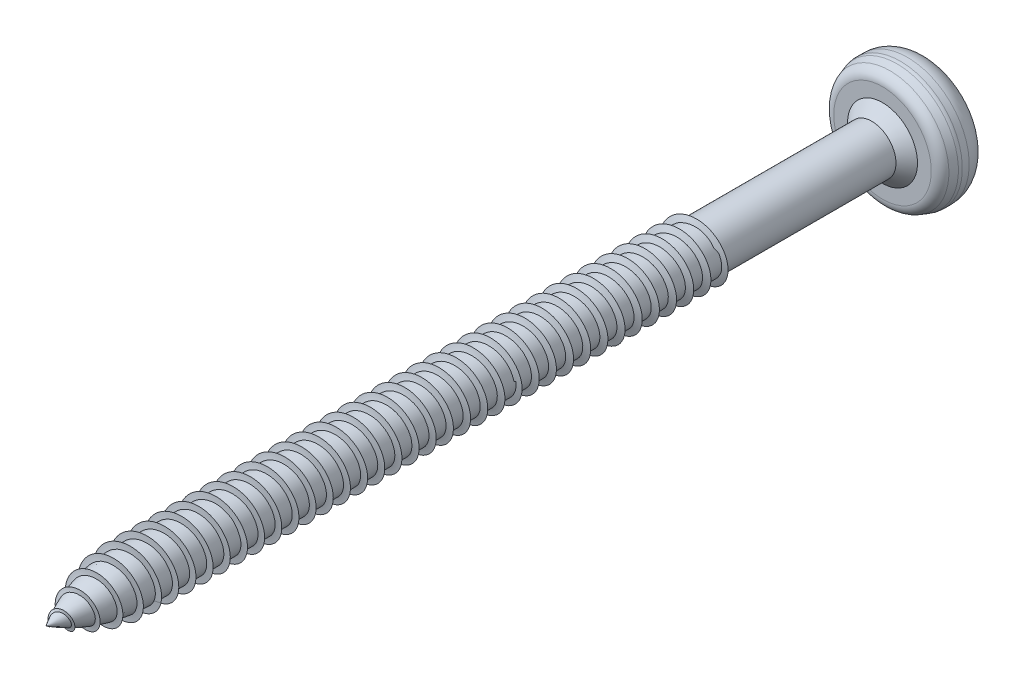
SolidWorks part; units mm, degrees
material "Rostfreier Stahl (ferritisch)"
ref_plane "Ebene vorne" through (0, 0, 0) normal (0, 0, 1) x (1, 0, 0)
ref_plane "Ebene oben" through (0, 0, 0) normal (0, 1, 0) x (1, 0, 0)
ref_plane "Ebene rechts" through (0, 0, 0) normal (1, 0, 0) x (0, 0, -1)
sketch "Skizze1" plane through (0, 0, 0) normal (1, 0, 0) x (0, 0, -1)
  line L0 (0, 0) -> (-87.1393, 0) construction
  line L1 (-0.0068, 3.4746) -> (-0.9378, 0)
  line L2 (-74, 2.25) -> (-5.3, 2.25)
  line L3 (-5.3, 2.25) -> (-4.3, 3.25)
  line L4 (-4.3, 3.25) -> (-4.3, 4.5292)
  line L5 (0, 3.75) -> (0, 3.5263)
  line L6 (-0.9378, 0) -> (-82, 0)
  line L7 (-3.6162, 5.4779) -> (-2.954, 5.6987)
  line L8 (-2.6377, 5.75) -> (-2, 5.75)
  arc A0 (-74, 2.25) -> (-82, 0) centre (-74, -13.0972) ccw
  arc A1 (-2.6377, 5.75) -> (-2.954, 5.6987) centre (-2.6377, 4.75) ccw
  arc A2 (-2, 5.75) -> (0, 3.75) centre (-2, 3.75) cw
  arc A3 (-4.3, 4.5292) -> (-3.6162, 5.4779) centre (-3.3, 4.5292) cw
  arc A5 (-0.0068, 3.4746) -> (0, 3.5263) centre (-0.2, 3.5263) ccw
  point P14 (0, 5.75)
  point P15 (-2.8, 5.75)
  point P19 (-4.3, 5.25)
  point P25 (0, 3.5)
  dimension "D8" = 0.5
  dimension "D9" = 2
  dimension "D12" = 0.2
  dimension "D14" = 1
  dimension "D1" = 45
  dimension "D2" = 1
  dimension "D3" = 11.5
  dimension "D4" = 4.3
  dimension "D5" = 4.5
  dimension "D6" = 8
  dimension "D7" = 82
  dimension "D10" = 15
  dimension "D11" = 7
  dimension "D13" = 1.5
revolve "Rotation1" add sketch "Skizze1" angle 360 about L0
ref_plane "Ebene5" through (0, 0, 82) normal (0, 0, 1) x (1, 0, 0)
sketch "Skizze15" plane through (0, 0, 0) normal (1, 0, 0) x (0, 0, -1)
  line L0 (-82, 0) -> (-20, 0)
  line L1 (-82, 6.325) -> (-82, -6.325) construction
  point P6 (-82, 0)
  dimension "D1" = 62
sketch "Skizze29" plane through (0, 0, 0) normal (1, 0, 0) x (0, 0, -1)
  line L1 (-74, 1.75) -> (-5.3, 1.75)
  line L2 (-5.3, 2.25) -> (-74, 2.25) construction
  line L3 (-74, 2.25) -> (-74, -2.25) construction
  line L4 (-5.3, 2.25) -> (-5.3, -2.25) construction
  arc A1 (-74, 1.75) -> (-82, 0) centre (-74, -17.4107) ccw
  dimension "D1" = 0.5
surface "Oberfläche-Rotation3" sketch "Skizze29" parameters "D1"=360
sketch "Skizze18" plane through (0, 0, 0) normal (1, 0, 0) x (0, 0, -1)
  line L1 (0, 0) -> (-82, 0) construction
  line L2 (-5.3, 2.8) -> (-74, 2.8)
  line L3 (-5.3, 2.8) -> (-74, 2.8)
  line L4 (-82, 6.325) -> (-82, -6.325) construction
  arc A0 (-74, 2.8) -> (-82, 0) centre (-74, -10.0286) ccw
  dimension "D2" = 5.6
  dimension "D1" = 0.55
surface "Oberfläche-Rotation2" sketch "Skizze18" parameters "D1"=360
sketch "Skizze27" plane through (0, 0, 82) normal (0, 0, 1) x (1, 0, 0)
  line L0 (0, 0) -> (0, 4)
  line L1 (0, 0) -> (3.9392, -0.6946)
  line L2 (0, 0) -> (-1.3681, -3.7588)
  circle A0 centre (0, 0) radius 4
  dimension "D1" = 8
  dimension "D2" = 100
  dimension "D3" = 100
surface "Oberfläche-Austragung13" parameters "D0"=14000
surface "Oberfläche-Trimmen6"
surface "Oberfläche-Trimmen7"
sketch "Skizze34" plane through (0, 0, 0) normal (1, 0, 0) x (0, 0, -1)
  line L0 (-82, 0) -> (-21.0647, 0)
  line L1 (-21.0647, 0) -> (-21.0647, -2.8)
  line L2 (-21.5039, -2.8) -> (-20.62, -2.8)
  spline S0 degree 2 poles (-20.0018, 1.3999) (-20.048, 1.8275) (-20.0886, 2.1449) (-20.2214, 3.184) (-20.3543, 2.6311) (-20.4871, 2.0782) (-20.62, 0.4862) (-20.7529, -1.1058) (-20.8857, -2.1449) (-21.0186, -3.184) (-21.1514, -2.6311) (-21.2843, -2.0782) (-21.4171, -0.4862) (-21.55, 1.1058) (-21.6829, 2.1449) (-21.8157, 3.184) (-21.9486, 2.6311) (-22.0814, 2.0782) (-22.2143, 0.4862) (-22.3471, -1.1058) (-22.48, -2.1449) (-22.6129, -3.184) (-22.7457, -2.6311) (-22.8786, -2.0782) (-23.0114, -0.4862) (-23.1443, 1.1058) (-23.2771, 2.1449) (-23.41, 3.184) (-23.5429, 2.6311) (-23.6757, 2.0782) (-23.8086, 0.4862) (-23.9414, -1.1058) (-24.0743, -2.1449) (-24.2071, -3.184) (-24.34, -2.6311) (-24.4729, -2.0782) (-24.6057, -0.4862) (-24.7386, 1.1058) (-24.8714, 2.1449) (-25.0043, 3.184) (-25.1371, 2.6311) (-25.27, 2.0782) (-25.4029, 0.4862) (-25.5357, -1.1058) (-25.6686, -2.1449) (-25.8014, -3.184) (-25.9343, -2.6311) (-26.0671, -2.0782) (-26.2, -0.4862) (-26.3329, 1.1058) (-26.4657, 2.1449) (-26.5986, 3.184) (-26.7314, 2.6311) (-26.8643, 2.0782) (-26.9971, 0.4862) (-27.13, -1.1058) (-27.2629, -2.1449) (-27.3957, -3.184) (-27.5286, -2.6311) (-27.6614, -2.0782) (-27.7943, -0.4862) (-27.9271, 1.1058) (-28.06, 2.1449) (-28.1929, 3.184) (-28.3257, 2.6311) (-28.4586, 2.0782) (-28.5914, 0.4862) (-28.7243, -1.1058) (-28.8571, -2.1449) (-28.99, -3.184) (-29.1229, -2.6311) (-29.2557, -2.0782) (-29.3886, -0.4862) (-29.5214, 1.1058) (-29.6543, 2.1449) (-29.7871, 3.184) (-29.92, 2.6311) (-30.0529, 2.0782) (-30.1857, 0.4862) (-30.3186, -1.1058) (-30.4514, -2.1449) (-30.5843, -3.184) (-30.7171, -2.6311) (-30.85, -2.0782) (-30.9829, -0.4862) (-31.1157, 1.1058) (-31.2486, 2.1449) (-31.3814, 3.184) (-31.5143, 2.6311) (-31.6471, 2.0782) (-31.78, 0.4862) (-31.9129, -1.1058) (-32.0457, -2.1449) (-32.1786, -3.184) (-32.3114, -2.6311) (-32.4443, -2.0782) (-32.5771, -0.4862) (-32.71, 1.1058) (-32.8429, 2.1449) (-32.9757, 3.184) (-33.1086, 2.6311) (-33.2414, 2.0782) (-33.3743, 0.4862) (-33.5071, -1.1058) (-33.64, -2.1449) (-33.7729, -3.184) (-33.9057, -2.6311) (-34.0386, -2.0782) (-34.1714, -0.4862) (-34.3043, 1.1058) (-34.4371, 2.1449) (-34.57, 3.184) (-34.7029, 2.6311) (-34.8357, 2.0782) (-34.9686, 0.4862) (-35.1014, -1.1058) (-35.2343, -2.1449) (-35.3671, -3.184) (-35.5, -2.6311) (-35.6329, -2.0782) (-35.7657, -0.4862) (-35.8986, 1.1058) (-36.0314, 2.1449) (-36.1643, 3.184) (-36.2971, 2.6311) (-36.43, 2.0782) (-36.5629, 0.4862) (-36.6957, -1.1058) (-36.8286, -2.1449) (-36.9614, -3.184) (-37.0943, -2.6311) (-37.2271, -2.0782) (-37.36, -0.4862) (-37.4929, 1.1058) (-37.6257, 2.1449) (-37.7586, 3.184) (-37.8914, 2.6311) (-38.0243, 2.0782) (-38.1571, 0.4862) (-38.29, -1.1058) (-38.4229, -2.1449) (-38.5557, -3.184) (-38.6886, -2.6311) (-38.8214, -2.0782) (-38.9543, -0.4862) (-39.0871, 1.1058) (-39.22, 2.1449) (-39.3529, 3.184) (-39.4857, 2.6311) (-39.6186, 2.0782) (-39.7514, 0.4862) (-39.8843, -1.1058) (-40.0171, -2.1449) (-40.15, -3.184) (-40.2829, -2.6311) (-40.4157, -2.0782) (-40.5486, -0.4862) (-40.6814, 1.1058) (-40.8143, 2.1449) (-40.9471, 3.184) (-41.08, 2.6311) (-41.2129, 2.0782) (-41.3457, 0.4862) (-41.4786, -1.1058) (-41.6114, -2.1449) (-41.7443, -3.184) (-41.8771, -2.6311) (-42.01, -2.0782) (-42.1429, -0.4862) (-42.2757, 1.1058) (-42.4086, 2.1449) (-42.5414, 3.184) (-42.6743, 2.6311) (-42.8071, 2.0782) (-42.94, 0.4862) (-43.0729, -1.1058) (-43.2057, -2.1449) (-43.3386, -3.184) (-43.4714, -2.6311) (-43.6043, -2.0782) (-43.7371, -0.4862) (-43.87, 1.1058) (-44.0029, 2.1449) (-44.1357, 3.184) (-44.2686, 2.6311) (-44.4014, 2.0782) (-44.5343, 0.4862) (-44.6671, -1.1058) (-44.8, -2.1449) (-44.9329, -3.184) (-45.0657, -2.6311) (-45.1986, -2.0782) (-45.3314, -0.4862) (-45.4643, 1.1058) (-45.5971, 2.1449) (-45.73, 3.184) (-45.8629, 2.6311) (-45.9957, 2.0782) (-46.1286, 0.4862) (-46.2614, -1.1058) (-46.3943, -2.1449) (-46.5271, -3.184) (-46.66, -2.6311) (-46.7929, -2.0782) (-46.9257, -0.4862) (-47.0586, 1.1058) (-47.1914, 2.1449) (-47.3243, 3.184) (-47.4571, 2.6311) (-47.59, 2.0782) (-47.7229, 0.4862) (-47.8557, -1.1058) (-47.9886, -2.1449) (-48.1214, -3.184) (-48.2543, -2.6311) (-48.3871, -2.0782) (-48.52, -0.4862) (-48.6529, 1.1058) (-48.7857, 2.1449) (-48.9186, 3.184) (-49.0514, 2.6311) (-49.1843, 2.0782) (-49.3171, 0.4862) (-49.45, -1.1058) (-49.5829, -2.1449) (-49.7157, -3.184) (-49.8486, -2.6311) (-49.9814, -2.0782) (-50.1143, -0.4862) (-50.2471, 1.1058) (-50.38, 2.1449) (-50.5129, 3.184) (-50.6457, 2.6311) (-50.7786, 2.0782) (-50.9114, 0.4862) (-51.0443, -1.1058) (-51.1771, -2.1449) (-51.31, -3.184) (-51.4429, -2.6311) (-51.5757, -2.0782) (-51.7086, -0.4862) (-51.8414, 1.1058) (-51.9743, 2.1449) (-52.1071, 3.184) (-52.24, 2.6311) (-52.3729, 2.0782) (-52.5057, 0.4862) (-52.6386, -1.1058) (-52.7714, -2.1449) (-52.9043, -3.184) (-53.0371, -2.6311) (-53.17, -2.0782) (-53.3029, -0.4862) (-53.4357, 1.1058) (-53.5686, 2.1449) (-53.7014, 3.184) (-53.8343, 2.6311) (-53.9671, 2.0782) (-54.1, 0.4862) (-54.2329, -1.1058) (-54.3657, -2.1449) (-54.4986, -3.184) (-54.6314, -2.6311) (-54.7643, -2.0782) (-54.8971, -0.4862) (-55.03, 1.1058) (-55.1629, 2.1449) (-55.2957, 3.184) (-55.4286, 2.6311) (-55.5614, 2.0782) (-55.6943, 0.4862) (-55.8271, -1.1058) (-55.96, -2.1449) (-56.0929, -3.184) (-56.2257, -2.6311) (-56.3586, -2.0782) (-56.4914, -0.4862) (-56.6243, 1.1058) (-56.7571, 2.1449) (-56.89, 3.184) (-57.0229, 2.6311) (-57.1557, 2.0782) (-57.2886, 0.4862) (-57.4214, -1.1058) (-57.5543, -2.1449) (-57.6871, -3.184) (-57.82, -2.6311) (-57.9529, -2.0782) (-58.0857, -0.4862) (-58.2186, 1.1058) (-58.3514, 2.1449) (-58.4843, 3.184) (-58.6171, 2.6311) (-58.75, 2.0782) (-58.8829, 0.4862) (-59.0157, -1.1058) (-59.1486, -2.1449) (-59.2814, -3.184) (-59.4143, -2.6311) (-59.5471, -2.0782) (-59.68, -0.4862) (-59.8129, 1.1058) (-59.9457, 2.1449) (-60.0786, 3.184) (-60.2114, 2.6311) (-60.3443, 2.0782) (-60.4771, 0.4862) (-60.61, -1.1058) (-60.7429, -2.1449) (-60.8757, -3.184) (-61.0086, -2.6311) (-61.1414, -2.0782) (-61.2743, -0.4862) (-61.4071, 1.1058) (-61.54, 2.1449) (-61.6729, 3.184) (-61.8057, 2.6311) (-61.9386, 2.0782) (-62.0714, 0.4862) (-62.2043, -1.1058) (-62.3371, -2.1449) (-62.47, -3.184) (-62.6029, -2.6311) (-62.7357, -2.0782) (-62.8686, -0.4862) (-63.0014, 1.1058) (-63.1343, 2.1449) (-63.2671, 3.184) (-63.4, 2.6311) (-63.5329, 2.0782) (-63.6657, 0.4862) (-63.7986, -1.1058) (-63.9314, -2.1449) (-64.0643, -3.184) (-64.1971, -2.6311) (-64.33, -2.0782) (-64.4629, -0.4862) (-64.5957, 1.1058) (-64.7286, 2.1449) (-64.8614, 3.184) (-64.9943, 2.6311) (-65.1271, 2.0782) (-65.26, 0.4862) (-65.3929, -1.1058) (-65.5257, -2.1449) (-65.6586, -3.184) (-65.7914, -2.6311) (-65.9243, -2.0782) (-66.0571, -0.4862) (-66.19, 1.1058) (-66.3229, 2.1449) (-66.4557, 3.184) (-66.5886, 2.6311) (-66.7214, 2.0782) (-66.8543, 0.4862) (-66.9871, -1.1058) (-67.12, -2.1449) (-67.2529, -3.184) (-67.3857, -2.6311) (-67.5186, -2.0782) (-67.6514, -0.4862) (-67.7843, 1.1058) (-67.9171, 2.1449) (-68.05, 3.184) (-68.1829, 2.6311) (-68.3157, 2.0782) (-68.4486, 0.4862) (-68.5814, -1.1058) (-68.7143, -2.1449) (-68.8471, -3.184) (-68.98, -2.6311) (-69.1129, -2.0782) (-69.2457, -0.4862) (-69.3786, 1.1058) (-69.5114, 2.1449) (-69.6443, 3.184) (-69.7771, 2.6311) (-69.91, 2.0782) (-70.0429, 0.4862) (-70.1757, -1.1058) (-70.3086, -2.1449) (-70.4414, -3.184) (-70.5743, -2.6311) (-70.7071, -2.0782) (-70.84, -0.4862) (-70.9729, 1.1058) (-71.1057, 2.1449) (-71.2386, 3.184) (-71.3714, 2.6311) (-71.5043, 2.0782) (-71.6371, 0.4862) (-71.77, -1.1058) (-71.9029, -2.1449) (-72.0357, -3.184) (-72.1686, -2.6311) (-72.3014, -2.0782) (-72.4343, -0.4862) (-72.5671, 1.1058) (-72.7, 2.1449) (-72.8329, 3.184) (-72.9657, 2.6311) (-73.0986, 2.0782) (-73.2314, 0.4862) (-73.3643, -1.1058) (-73.4971, -2.1449) (-73.63, -3.184) (-73.7629, -2.6311) (-73.8779, -2.1525) (-74, -0.8136) knots 0.128712 0.128712 0.128712 0.130151 0.130151 0.134424 0.134424 0.138698 0.138698 0.142971 0.142971 0.147245 0.147245 0.151518 0.151518 0.155792 0.155792 0.160065 0.160065 0.164339 0.164339 0.168612 0.168612 0.172886 0.172886 0.177159 0.177159 0.181433 0.181433 0.185706 0.185706 0.18998 0.18998 0.194253 0.194253 0.198527 0.198527 0.2028 0.2028 0.207074 0.207074 0.211347 0.211347 0.215621 0.215621 0.219894 0.219894 0.224168 0.224168 0.228441 0.228441 0.232715 0.232715 0.236988 0.236988 0.241262 0.241262 0.245535 0.245535 0.249809 0.249809 0.254082 0.254082 0.258356 0.258356 0.262629 0.262629 0.266903 0.266903 0.271176 0.271176 0.27545 0.27545 0.279723 0.279723 0.283997 0.283997 0.28827 0.28827 0.292544 0.292544 0.296817 0.296817 0.301091 0.301091 0.305364 0.305364 0.309638 0.309638 0.313911 0.313911 0.318185 0.318185 0.322458 0.322458 0.326732 0.326732 0.331005 0.331005 0.335279 0.335279 0.339553 0.339553 0.343826 0.343826 0.3481 0.3481 0.352373 0.352373 0.356647 0.356647 0.36092 0.36092 0.365194 0.365194 0.369467 0.369467 0.373741 0.373741 0.378014 0.378014 0.382288 0.382288 0.386561 0.386561 0.390835 0.390835 0.395108 0.395108 0.399382 0.399382 0.403655 0.403655 0.407929 0.407929 0.412202 0.412202 0.416476 0.416476 0.420749 0.420749 0.425023 0.425023 0.429296 0.429296 0.43357 0.43357 0.437843 0.437843 0.442117 0.442117 0.44639 0.44639 0.450664 0.450664 0.454937 0.454937 0.459211 0.459211 0.463484 0.463484 0.467758 0.467758 0.472031 0.472031 0.476305 0.476305 0.480578 0.480578 0.484852 0.484852 0.489125 0.489125 0.493399 0.493399 0.497672 0.497672 0.501946 0.501946 0.506219 0.506219 0.510493 0.510493 0.514766 0.514766 0.51904 0.51904 0.523313 0.523313 0.527587 0.527587 0.53186 0.53186 0.536134 0.536134 0.540407 0.540407 0.544681 0.544681 0.548954 0.548954 0.553228 0.553228 0.557501 0.557501 0.561775 0.561775 0.566048 0.566048 0.570322 0.570322 0.574595 0.574595 0.578869 0.578869 0.583142 0.583142 0.587416 0.587416 0.591689 0.591689 0.595963 0.595963 0.600236 0.600236 0.60451 0.60451 0.608783 0.608783 0.613057 0.613057 0.61733 0.61733 0.621604 0.621604 0.625877 0.625877 0.630151 0.630151 0.634424 0.634424 0.638698 0.638698 0.642971 0.642971 0.647245 0.647245 0.651518 0.651518 0.655792 0.655792 0.660065 0.660065 0.664339 0.664339 0.668612 0.668612 0.672886 0.672886 0.677159 0.677159 0.681433 0.681433 0.685706 0.685706 0.68998 0.68998 0.694253 0.694253 0.698527 0.698527 0.7028 0.7028 0.707074 0.707074 0.711347 0.711347 0.715621 0.715621 0.719894 0.719894 0.724168 0.724168 0.728441 0.728441 0.732715 0.732715 0.736988 0.736988 0.741262 0.741262 0.745535 0.745535 0.749809 0.749809 0.754082 0.754082 0.758356 0.758356 0.762629 0.762629 0.766903 0.766903 0.771176 0.771176 0.77545 0.77545 0.779723 0.779723 0.783997 0.783997 0.78827 0.78827 0.792544 0.792544 0.796817 0.796817 0.801091 0.801091 0.805364 0.805364 0.809638 0.809638 0.813911 0.813911 0.818185 0.818185 0.822458 0.822458 0.826732 0.826732 0.831005 0.831005 0.835279 0.835279 0.839553 0.839553 0.843826 0.843826 0.8481 0.8481 0.852373 0.852373 0.856647 0.856647 0.86092 0.86092 0.865194 0.865194 0.869467 0.869467 0.873741 0.873741 0.878014 0.878014 0.882288 0.882288 0.886561 0.886561 0.890835 0.890835 0.895108 0.895108 0.899382 0.899382 0.903655 0.903655 0.907929 0.907929 0.912202 0.912202 0.916476 0.916476 0.920749 0.920749 0.925023 0.925023 0.929296 0.929296 0.93357 0.93357 0.937843 0.937843 0.942117 0.942117 0.94639 0.94639 0.950664 0.950664 0.954937 0.954937 0.959211 0.959211 0.963484 0.963484 0.967758 0.967758 0.972031 0.972031 0.976305 0.976305 0.980578 0.980578 0.984852 0.984852 0.989125 0.989125 0.993399 0.993399 0.997166 0.997166 0.997166 weights 0.940152 0.954881 1 0.866025 1 0.866025 1 0.866025 1 0.866025 1 0.866025 1 0.866025 1 0.866025 1 0.866025 1 0.866025 1 0.866025 1 0.866025 1 0.866025 1 0.866025 1 0.866025 1 0.866025 1 0.866025 1 0.866025 1 0.866025 1 0.866025 1 0.866025 1 0.866025 1 0.866025 1 0.866025 1 0.866025 1 0.866025 1 0.866025 1 0.866025 1 0.866025 1 0.866025 1 0.866025 1 0.866025 1 0.866025 1 0.866025 1 0.866025 1 0.866025 1 0.866025 1 0.866025 1 0.866025 1 0.866025 1 0.866025 1 0.866025 1 0.866025 1 0.866025 1 0.866025 1 0.866025 1 0.866025 1 0.866025 1 0.866025 1 0.866025 1 0.866025 1 0.866025 1 0.866025 1 0.866025 1 0.866025 1 0.866025 1 0.866025 1 0.866025 1 0.866025 1 0.866025 1 0.866025 1 0.866025 1 0.866025 1 0.866025 1 0.866025 1 0.866025 1 0.866025 1 0.866025 1 0.866025 1 0.866025 1 0.866025 1 0.866025 1 0.866025 1 0.866025 1 0.866025 1 0.866025 1 0.866025 1 0.866025 1 0.866025 1 0.866025 1 0.866025 1 0.866025 1 0.866025 1 0.866025 1 0.866025 1 0.866025 1 0.866025 1 0.866025 1 0.866025 1 0.866025 1 0.866025 1 0.866025 1 0.866025 1 0.866025 1 0.866025 1 0.866025 1 0.866025 1 0.866025 1 0.866025 1 0.866025 1 0.866025 1 0.866025 1 0.866025 1 0.866025 1 0.866025 1 0.866025 1 0.866025 1 0.866025 1 0.866025 1 0.866025 1 0.866025 1 0.866025 1 0.866025 1 0.866025 1 0.866025 1 0.866025 1 0.866025 1 0.866025 1 0.866025 1 0.866025 1 0.866025 1 0.866025 1 0.866025 1 0.866025 1 0.866025 1 0.866025 1 0.866025 1 0.866025 1 0.866025 1 0.866025 1 0.866025 1 0.866025 1 0.866025 1 0.866025 1 0.866025 1 0.866025 1 0.866025 1 0.866025 1 0.866025 1 0.866025 1 0.866025 1 0.866025 1 0.866025 1 0.866025 1 0.866025 1 0.866025 1 0.866025 1 0.866025 1 0.866025 1 0.866025 1 0.866025 1 0.866025 1 0.866025 1 0.866025 1 0.866025 1 0.866025 1 0.866025 1 0.866025 1 0.866025 1 0.866025 1 0.866025 1 0.866025 1 0.866025 1 0.866025 1 0.866025 1 0.866025 1 0.866025 1 0.866025 1 0.866025 1 0.866025 1 0.866025 1 0.866025 1 0.866025 1 0.866025 1 0.866025 1 0.866025 1 0.866025 1 0.866025 1 0.866025 1 0.866025 1 0.866025 1 0.866025 1 0.866025 1 0.866025 1 0.866025 1 0.866025 1 0.866025 1 0.866025 1 0.866025 1 0.866025 1 0.866025 1 0.866025 1 0.866025 1 0.866025 1 0.866025 1 0.866025 1 0.866025 1 0.866025 1 0.866025 1 0.866025 1 0.866025 1 0.866025 1 0.866025 1 0.881903 0.972008 construction
  spline S1 degree 2 poles (-74, -2.4972) (-73.8779, -1.8643) (-73.7629, -0.4862) (-73.63, 1.1058) (-73.4971, 2.1449) (-73.3643, 3.184) (-73.2314, 2.6311) (-73.0986, 2.0782) (-72.9657, 0.4862) (-72.8329, -1.1058) (-72.7, -2.1449) (-72.5671, -3.184) (-72.4343, -2.6311) (-72.3014, -2.0782) (-72.1686, -0.4862) (-72.0357, 1.1058) (-71.9029, 2.1449) (-71.77, 3.184) (-71.6371, 2.6311) (-71.5043, 2.0782) (-71.3714, 0.4862) (-71.2386, -1.1058) (-71.1057, -2.1449) (-70.9729, -3.184) (-70.84, -2.6311) (-70.7071, -2.0782) (-70.5743, -0.4862) (-70.4414, 1.1058) (-70.3086, 2.1449) (-70.1757, 3.184) (-70.0429, 2.6311) (-69.91, 2.0782) (-69.7771, 0.4862) (-69.6443, -1.1058) (-69.5114, -2.1449) (-69.3786, -3.184) (-69.2457, -2.6311) (-69.1129, -2.0782) (-68.98, -0.4862) (-68.8471, 1.1058) (-68.7143, 2.1449) (-68.5814, 3.184) (-68.4486, 2.6311) (-68.3157, 2.0782) (-68.1829, 0.4862) (-68.05, -1.1058) (-67.9171, -2.1449) (-67.7843, -3.184) (-67.6514, -2.6311) (-67.5186, -2.0782) (-67.3857, -0.4862) (-67.2529, 1.1058) (-67.12, 2.1449) (-66.9871, 3.184) (-66.8543, 2.6311) (-66.7214, 2.0782) (-66.5886, 0.4862) (-66.4557, -1.1058) (-66.3229, -2.1449) (-66.19, -3.184) (-66.0571, -2.6311) (-65.9243, -2.0782) (-65.7914, -0.4862) (-65.6586, 1.1058) (-65.5257, 2.1449) (-65.3929, 3.184) (-65.26, 2.6311) (-65.1271, 2.0782) (-64.9943, 0.4862) (-64.8614, -1.1058) (-64.7286, -2.1449) (-64.5957, -3.184) (-64.4629, -2.6311) (-64.33, -2.0782) (-64.1971, -0.4862) (-64.0643, 1.1058) (-63.9314, 2.1449) (-63.7986, 3.184) (-63.6657, 2.6311) (-63.5329, 2.0782) (-63.4, 0.4862) (-63.2671, -1.1058) (-63.1343, -2.1449) (-63.0014, -3.184) (-62.8686, -2.6311) (-62.7357, -2.0782) (-62.6029, -0.4862) (-62.47, 1.1058) (-62.3371, 2.1449) (-62.2043, 3.184) (-62.0714, 2.6311) (-61.9386, 2.0782) (-61.8057, 0.4862) (-61.6729, -1.1058) (-61.54, -2.1449) (-61.4071, -3.184) (-61.2743, -2.6311) (-61.1414, -2.0782) (-61.0086, -0.4862) (-60.8757, 1.1058) (-60.7429, 2.1449) (-60.61, 3.184) (-60.4771, 2.6311) (-60.3443, 2.0782) (-60.2114, 0.4862) (-60.0786, -1.1058) (-59.9457, -2.1449) (-59.8129, -3.184) (-59.68, -2.6311) (-59.5471, -2.0782) (-59.4143, -0.4862) (-59.2814, 1.1058) (-59.1486, 2.1449) (-59.0157, 3.184) (-58.8829, 2.6311) (-58.75, 2.0782) (-58.6171, 0.4862) (-58.4843, -1.1058) (-58.3514, -2.1449) (-58.2186, -3.184) (-58.0857, -2.6311) (-57.9529, -2.0782) (-57.82, -0.4862) (-57.6871, 1.1058) (-57.5543, 2.1449) (-57.4214, 3.184) (-57.2886, 2.6311) (-57.1557, 2.0782) (-57.0229, 0.4862) (-56.89, -1.1058) (-56.7571, -2.1449) (-56.6243, -3.184) (-56.4914, -2.6311) (-56.3586, -2.0782) (-56.2257, -0.4862) (-56.0929, 1.1058) (-55.96, 2.1449) (-55.8271, 3.184) (-55.6943, 2.6311) (-55.5614, 2.0782) (-55.4286, 0.4862) (-55.2957, -1.1058) (-55.1629, -2.1449) (-55.03, -3.184) (-54.8971, -2.6311) (-54.7643, -2.0782) (-54.6314, -0.4862) (-54.4986, 1.1058) (-54.3657, 2.1449) (-54.2329, 3.184) (-54.1, 2.6311) (-53.9671, 2.0782) (-53.8343, 0.4862) (-53.7014, -1.1058) (-53.5686, -2.1449) (-53.4357, -3.184) (-53.3029, -2.6311) (-53.17, -2.0782) (-53.0371, -0.4862) (-52.9043, 1.1058) (-52.7714, 2.1449) (-52.6386, 3.184) (-52.5057, 2.6311) (-52.3729, 2.0782) (-52.24, 0.4862) (-52.1071, -1.1058) (-51.9743, -2.1449) (-51.8414, -3.184) (-51.7086, -2.6311) (-51.5757, -2.0782) (-51.4429, -0.4862) (-51.31, 1.1058) (-51.1771, 2.1449) (-51.0443, 3.184) (-50.9114, 2.6311) (-50.7786, 2.0782) (-50.6457, 0.4862) (-50.5129, -1.1058) (-50.38, -2.1449) (-50.2471, -3.184) (-50.1143, -2.6311) (-49.9814, -2.0782) (-49.8486, -0.4862) (-49.7157, 1.1058) (-49.5829, 2.1449) (-49.45, 3.184) (-49.3171, 2.6311) (-49.1843, 2.0782) (-49.0514, 0.4862) (-48.9186, -1.1058) (-48.7857, -2.1449) (-48.6529, -3.184) (-48.52, -2.6311) (-48.3871, -2.0782) (-48.2543, -0.4862) (-48.1214, 1.1058) (-47.9886, 2.1449) (-47.8557, 3.184) (-47.7229, 2.6311) (-47.59, 2.0782) (-47.4571, 0.4862) (-47.3243, -1.1058) (-47.1914, -2.1449) (-47.0586, -3.184) (-46.9257, -2.6311) (-46.7929, -2.0782) (-46.66, -0.4862) (-46.5271, 1.1058) (-46.3943, 2.1449) (-46.2614, 3.184) (-46.1286, 2.6311) (-45.9957, 2.0782) (-45.8629, 0.4862) (-45.73, -1.1058) (-45.5971, -2.1449) (-45.4643, -3.184) (-45.3314, -2.6311) (-45.1986, -2.0782) (-45.0657, -0.4862) (-44.9329, 1.1058) (-44.8, 2.1449) (-44.6671, 3.184) (-44.5343, 2.6311) (-44.4014, 2.0782) (-44.2686, 0.4862) (-44.1357, -1.1058) (-44.0029, -2.1449) (-43.87, -3.184) (-43.7371, -2.6311) (-43.6043, -2.0782) (-43.4714, -0.4862) (-43.3386, 1.1058) (-43.2057, 2.1449) (-43.0729, 3.184) (-42.94, 2.6311) (-42.8071, 2.0782) (-42.6743, 0.4862) (-42.5414, -1.1058) (-42.4086, -2.1449) (-42.2757, -3.184) (-42.1429, -2.6311) (-42.01, -2.0782) (-41.8771, -0.4862) (-41.7443, 1.1058) (-41.6114, 2.1449) (-41.4786, 3.184) (-41.3457, 2.6311) (-41.2129, 2.0782) (-41.08, 0.4862) (-40.9471, -1.1058) (-40.8143, -2.1449) (-40.6814, -3.184) (-40.5486, -2.6311) (-40.4157, -2.0782) (-40.2829, -0.4862) (-40.15, 1.1058) (-40.0171, 2.1449) (-39.8843, 3.184) (-39.7514, 2.6311) (-39.6186, 2.0782) (-39.4857, 0.4862) (-39.3529, -1.1058) (-39.22, -2.1449) (-39.0871, -3.184) (-38.9543, -2.6311) (-38.8214, -2.0782) (-38.6886, -0.4862) (-38.5557, 1.1058) (-38.4229, 2.1449) (-38.29, 3.184) (-38.1571, 2.6311) (-38.0243, 2.0782) (-37.8914, 0.4862) (-37.7586, -1.1058) (-37.6257, -2.1449) (-37.4929, -3.184) (-37.36, -2.6311) (-37.2271, -2.0782) (-37.0943, -0.4862) (-36.9614, 1.1058) (-36.8286, 2.1449) (-36.6957, 3.184) (-36.5629, 2.6311) (-36.43, 2.0782) (-36.2971, 0.4862) (-36.1643, -1.1058) (-36.0314, -2.1449) (-35.8986, -3.184) (-35.7657, -2.6311) (-35.6329, -2.0782) (-35.5, -0.4862) (-35.3671, 1.1058) (-35.2343, 2.1449) (-35.1014, 3.184) (-34.9686, 2.6311) (-34.8357, 2.0782) (-34.7029, 0.4862) (-34.57, -1.1058) (-34.4371, -2.1449) (-34.3043, -3.184) (-34.1714, -2.6311) (-34.0386, -2.0782) (-33.9057, -0.4862) (-33.7729, 1.1058) (-33.64, 2.1449) (-33.5071, 3.184) (-33.3743, 2.6311) (-33.2414, 2.0782) (-33.1086, 0.4862) (-32.9757, -1.1058) (-32.8429, -2.1449) (-32.71, -3.184) (-32.5771, -2.6311) (-32.4443, -2.0782) (-32.3114, -0.4862) (-32.1786, 1.1058) (-32.0457, 2.1449) (-31.9129, 3.184) (-31.78, 2.6311) (-31.6471, 2.0782) (-31.5143, 0.4862) (-31.3814, -1.1058) (-31.2486, -2.1449) (-31.1157, -3.184) (-30.9829, -2.6311) (-30.85, -2.0782) (-30.7171, -0.4862) (-30.5843, 1.1058) (-30.4514, 2.1449) (-30.3186, 3.184) (-30.1857, 2.6311) (-30.0529, 2.0782) (-29.92, 0.4862) (-29.7871, -1.1058) (-29.6543, -2.1449) (-29.5214, -3.184) (-29.3886, -2.6311) (-29.2557, -2.0782) (-29.1229, -0.4862) (-28.99, 1.1058) (-28.8571, 2.1449) (-28.7243, 3.184) (-28.5914, 2.6311) (-28.4586, 2.0782) (-28.3257, 0.4862) (-28.1929, -1.1058) (-28.06, -2.1449) (-27.9271, -3.184) (-27.7943, -2.6311) (-27.6614, -2.0782) (-27.5286, -0.4862) (-27.3957, 1.1058) (-27.2629, 2.1449) (-27.13, 3.184) (-26.9971, 2.6311) (-26.8643, 2.0782) (-26.7314, 0.4862) (-26.5986, -1.1058) (-26.4657, -2.1449) (-26.3329, -3.184) (-26.2, -2.6311) (-26.0671, -2.0782) (-25.9343, -0.4862) (-25.8014, 1.1058) (-25.6686, 2.1449) (-25.5357, 3.184) (-25.4029, 2.6311) (-25.27, 2.0782) (-25.1371, 0.4862) (-25.0043, -1.1058) (-24.8714, -2.1449) (-24.7386, -3.184) (-24.6057, -2.6311) (-24.4729, -2.0782) (-24.34, -0.4862) (-24.2071, 1.1058) (-24.0743, 2.1449) (-23.9414, 3.184) (-23.8086, 2.6311) (-23.6757, 2.0782) (-23.5429, 0.4862) (-23.41, -1.1058) (-23.2771, -2.1449) (-23.1443, -3.184) (-23.0114, -2.6311) (-22.8786, -2.0782) (-22.7457, -0.4862) (-22.6129, 1.1058) (-22.48, 2.1449) (-22.3471, 3.184) (-22.2143, 2.6311) (-22.0814, 2.0782) (-21.9486, 0.4862) (-21.8157, -1.1058) (-21.6829, -2.1449) (-21.55, -3.184) (-21.4171, -2.6311) (-21.2843, -2.0782) (-21.1514, -0.4862) (-21.0186, 1.1058) (-20.8857, 2.1449) (-20.7529, 3.184) (-20.62, 2.6311) (-20.4871, 2.0782) (-20.3543, 0.4862) (-20.2214, -1.1058) (-20.0886, -2.1449) (-20.048, -2.4623) (-20.0018, -2.6312) knots 0.128712 0.128712 0.128712 0.132479 0.132479 0.136752 0.136752 0.141026 0.141026 0.145299 0.145299 0.149573 0.149573 0.153846 0.153846 0.15812 0.15812 0.162393 0.162393 0.166667 0.166667 0.17094 0.17094 0.175214 0.175214 0.179487 0.179487 0.183761 0.183761 0.188034 0.188034 0.192308 0.192308 0.196581 0.196581 0.200855 0.200855 0.205128 0.205128 0.209402 0.209402 0.213675 0.213675 0.217949 0.217949 0.222222 0.222222 0.226496 0.226496 0.230769 0.230769 0.235043 0.235043 0.239316 0.239316 0.24359 0.24359 0.247863 0.247863 0.252137 0.252137 0.25641 0.25641 0.260684 0.260684 0.264957 0.264957 0.269231 0.269231 0.273504 0.273504 0.277778 0.277778 0.282051 0.282051 0.286325 0.286325 0.290598 0.290598 0.294872 0.294872 0.299145 0.299145 0.303419 0.303419 0.307692 0.307692 0.311966 0.311966 0.316239 0.316239 0.320513 0.320513 0.324786 0.324786 0.32906 0.32906 0.333333 0.333333 0.337607 0.337607 0.34188 0.34188 0.346154 0.346154 0.350427 0.350427 0.354701 0.354701 0.358974 0.358974 0.363248 0.363248 0.367521 0.367521 0.371795 0.371795 0.376068 0.376068 0.380342 0.380342 0.384615 0.384615 0.388889 0.388889 0.393162 0.393162 0.397436 0.397436 0.401709 0.401709 0.405983 0.405983 0.410256 0.410256 0.41453 0.41453 0.418803 0.418803 0.423077 0.423077 0.42735 0.42735 0.431624 0.431624 0.435897 0.435897 0.440171 0.440171 0.444444 0.444444 0.448718 0.448718 0.452991 0.452991 0.457265 0.457265 0.461538 0.461538 0.465812 0.465812 0.470085 0.470085 0.474359 0.474359 0.478632 0.478632 0.482906 0.482906 0.487179 0.487179 0.491453 0.491453 0.495726 0.495726 0.5 0.5 0.504274 0.504274 0.508547 0.508547 0.512821 0.512821 0.517094 0.517094 0.521368 0.521368 0.525641 0.525641 0.529915 0.529915 0.534188 0.534188 0.538462 0.538462 0.542735 0.542735 0.547009 0.547009 0.551282 0.551282 0.555556 0.555556 0.559829 0.559829 0.564103 0.564103 0.568376 0.568376 0.57265 0.57265 0.576923 0.576923 0.581197 0.581197 0.58547 0.58547 0.589744 0.589744 0.594017 0.594017 0.598291 0.598291 0.602564 0.602564 0.606838 0.606838 0.611111 0.611111 0.615385 0.615385 0.619658 0.619658 0.623932 0.623932 0.628205 0.628205 0.632479 0.632479 0.636752 0.636752 0.641026 0.641026 0.645299 0.645299 0.649573 0.649573 0.653846 0.653846 0.65812 0.65812 0.662393 0.662393 0.666667 0.666667 0.67094 0.67094 0.675214 0.675214 0.679487 0.679487 0.683761 0.683761 0.688034 0.688034 0.692308 0.692308 0.696581 0.696581 0.700855 0.700855 0.705128 0.705128 0.709402 0.709402 0.713675 0.713675 0.717949 0.717949 0.722222 0.722222 0.726496 0.726496 0.730769 0.730769 0.735043 0.735043 0.739316 0.739316 0.74359 0.74359 0.747863 0.747863 0.752137 0.752137 0.75641 0.75641 0.760684 0.760684 0.764957 0.764957 0.769231 0.769231 0.773504 0.773504 0.777778 0.777778 0.782051 0.782051 0.786325 0.786325 0.790598 0.790598 0.794872 0.794872 0.799145 0.799145 0.803419 0.803419 0.807692 0.807692 0.811966 0.811966 0.816239 0.816239 0.820513 0.820513 0.824786 0.824786 0.82906 0.82906 0.833333 0.833333 0.837607 0.837607 0.84188 0.84188 0.846154 0.846154 0.850427 0.850427 0.854701 0.854701 0.858974 0.858974 0.863248 0.863248 0.867521 0.867521 0.871795 0.871795 0.876068 0.876068 0.880342 0.880342 0.884615 0.884615 0.888889 0.888889 0.893162 0.893162 0.897436 0.897436 0.901709 0.901709 0.905983 0.905983 0.910256 0.910256 0.91453 0.91453 0.918803 0.918803 0.923077 0.923077 0.92735 0.92735 0.931624 0.931624 0.935897 0.935897 0.940171 0.940171 0.944444 0.944444 0.948718 0.948718 0.952991 0.952991 0.957265 0.957265 0.961538 0.961538 0.965812 0.965812 0.970085 0.970085 0.974359 0.974359 0.978632 0.978632 0.982906 0.982906 0.987179 0.987179 0.991453 0.991453 0.995726 0.995726 0.997166 0.997166 0.997166 weights 0.972008 0.881903 1 0.866025 1 0.866025 1 0.866025 1 0.866025 1 0.866025 1 0.866025 1 0.866025 1 0.866025 1 0.866025 1 0.866025 1 0.866025 1 0.866025 1 0.866025 1 0.866025 1 0.866025 1 0.866025 1 0.866025 1 0.866025 1 0.866025 1 0.866025 1 0.866025 1 0.866025 1 0.866025 1 0.866025 1 0.866025 1 0.866025 1 0.866025 1 0.866025 1 0.866025 1 0.866025 1 0.866025 1 0.866025 1 0.866025 1 0.866025 1 0.866025 1 0.866025 1 0.866025 1 0.866025 1 0.866025 1 0.866025 1 0.866025 1 0.866025 1 0.866025 1 0.866025 1 0.866025 1 0.866025 1 0.866025 1 0.866025 1 0.866025 1 0.866025 1 0.866025 1 0.866025 1 0.866025 1 0.866025 1 0.866025 1 0.866025 1 0.866025 1 0.866025 1 0.866025 1 0.866025 1 0.866025 1 0.866025 1 0.866025 1 0.866025 1 0.866025 1 0.866025 1 0.866025 1 0.866025 1 0.866025 1 0.866025 1 0.866025 1 0.866025 1 0.866025 1 0.866025 1 0.866025 1 0.866025 1 0.866025 1 0.866025 1 0.866025 1 0.866025 1 0.866025 1 0.866025 1 0.866025 1 0.866025 1 0.866025 1 0.866025 1 0.866025 1 0.866025 1 0.866025 1 0.866025 1 0.866025 1 0.866025 1 0.866025 1 0.866025 1 0.866025 1 0.866025 1 0.866025 1 0.866025 1 0.866025 1 0.866025 1 0.866025 1 0.866025 1 0.866025 1 0.866025 1 0.866025 1 0.866025 1 0.866025 1 0.866025 1 0.866025 1 0.866025 1 0.866025 1 0.866025 1 0.866025 1 0.866025 1 0.866025 1 0.866025 1 0.866025 1 0.866025 1 0.866025 1 0.866025 1 0.866025 1 0.866025 1 0.866025 1 0.866025 1 0.866025 1 0.866025 1 0.866025 1 0.866025 1 0.866025 1 0.866025 1 0.866025 1 0.866025 1 0.866025 1 0.866025 1 0.866025 1 0.866025 1 0.866025 1 0.866025 1 0.866025 1 0.866025 1 0.866025 1 0.866025 1 0.866025 1 0.866025 1 0.866025 1 0.866025 1 0.866025 1 0.866025 1 0.866025 1 0.866025 1 0.866025 1 0.866025 1 0.866025 1 0.866025 1 0.866025 1 0.866025 1 0.866025 1 0.866025 1 0.866025 1 0.866025 1 0.866025 1 0.866025 1 0.866025 1 0.866025 1 0.866025 1 0.866025 1 0.866025 1 0.866025 1 0.866025 1 0.866025 1 0.866025 1 0.866025 1 0.866025 1 0.866025 1 0.866025 1 0.866025 1 0.866025 1 0.866025 1 0.866025 1 0.866025 1 0.866025 1 0.866025 1 0.866025 1 0.866025 1 0.866025 1 0.866025 1 0.866025 1 0.866025 1 0.866025 1 0.866025 1 0.866025 1 0.866025 1 0.866025 1 0.866025 1 0.866025 1 0.866025 1 0.866025 1 0.866025 1 0.866025 1 0.866025 1 0.866025 1 0.866025 1 0.954881 0.940152 construction
  spline S2 degree 2 poles (-74, 2.7798) (-73.8779, 2.6119) (-73.7629, 1.4) (-73.63, 0) (-73.4971, -1.4) (-73.3643, -2.8) (-73.2314, -2.8) (-73.0986, -2.8) (-72.9657, -1.4) (-72.8329, 0) (-72.7, 1.4) (-72.5671, 2.8) (-72.4343, 2.8) (-72.3014, 2.8) (-72.1686, 1.4) (-72.0357, 0) (-71.9029, -1.4) (-71.77, -2.8) (-71.6371, -2.8) (-71.5043, -2.8) (-71.3714, -1.4) (-71.2386, 0) (-71.1057, 1.4) (-70.9729, 2.8) (-70.84, 2.8) (-70.7071, 2.8) (-70.5743, 1.4) (-70.4414, 0) (-70.3086, -1.4) (-70.1757, -2.8) (-70.0429, -2.8) (-69.91, -2.8) (-69.7771, -1.4) (-69.6443, 0) (-69.5114, 1.4) (-69.3786, 2.8) (-69.2457, 2.8) (-69.1129, 2.8) (-68.98, 1.4) (-68.8471, 0) (-68.7143, -1.4) (-68.5814, -2.8) (-68.4486, -2.8) (-68.3157, -2.8) (-68.1829, -1.4) (-68.05, 0) (-67.9171, 1.4) (-67.7843, 2.8) (-67.6514, 2.8) (-67.5186, 2.8) (-67.3857, 1.4) (-67.2529, 0) (-67.12, -1.4) (-66.9871, -2.8) (-66.8543, -2.8) (-66.7214, -2.8) (-66.5886, -1.4) (-66.4557, 0) (-66.3229, 1.4) (-66.19, 2.8) (-66.0571, 2.8) (-65.9243, 2.8) (-65.7914, 1.4) (-65.6586, 0) (-65.5257, -1.4) (-65.3929, -2.8) (-65.26, -2.8) (-65.1271, -2.8) (-64.9943, -1.4) (-64.8614, 0) (-64.7286, 1.4) (-64.5957, 2.8) (-64.4629, 2.8) (-64.33, 2.8) (-64.1971, 1.4) (-64.0643, 0) (-63.9314, -1.4) (-63.7986, -2.8) (-63.6657, -2.8) (-63.5329, -2.8) (-63.4, -1.4) (-63.2671, 0) (-63.1343, 1.4) (-63.0014, 2.8) (-62.8686, 2.8) (-62.7357, 2.8) (-62.6029, 1.4) (-62.47, 0) (-62.3371, -1.4) (-62.2043, -2.8) (-62.0714, -2.8) (-61.9386, -2.8) (-61.8057, -1.4) (-61.6729, 0) (-61.54, 1.4) (-61.4071, 2.8) (-61.2743, 2.8) (-61.1414, 2.8) (-61.0086, 1.4) (-60.8757, 0) (-60.7429, -1.4) (-60.61, -2.8) (-60.4771, -2.8) (-60.3443, -2.8) (-60.2114, -1.4) (-60.0786, 0) (-59.9457, 1.4) (-59.8129, 2.8) (-59.68, 2.8) (-59.5471, 2.8) (-59.4143, 1.4) (-59.2814, 0) (-59.1486, -1.4) (-59.0157, -2.8) (-58.8829, -2.8) (-58.75, -2.8) (-58.6171, -1.4) (-58.4843, 0) (-58.3514, 1.4) (-58.2186, 2.8) (-58.0857, 2.8) (-57.9529, 2.8) (-57.82, 1.4) (-57.6871, 0) (-57.5543, -1.4) (-57.4214, -2.8) (-57.2886, -2.8) (-57.1557, -2.8) (-57.0229, -1.4) (-56.89, 0) (-56.7571, 1.4) (-56.6243, 2.8) (-56.4914, 2.8) (-56.3586, 2.8) (-56.2257, 1.4) (-56.0929, 0) (-55.96, -1.4) (-55.8271, -2.8) (-55.6943, -2.8) (-55.5614, -2.8) (-55.4286, -1.4) (-55.2957, 0) (-55.1629, 1.4) (-55.03, 2.8) (-54.8971, 2.8) (-54.7643, 2.8) (-54.6314, 1.4) (-54.4986, 0) (-54.3657, -1.4) (-54.2329, -2.8) (-54.1, -2.8) (-53.9671, -2.8) (-53.8343, -1.4) (-53.7014, 0) (-53.5686, 1.4) (-53.4357, 2.8) (-53.3029, 2.8) (-53.17, 2.8) (-53.0371, 1.4) (-52.9043, 0) (-52.7714, -1.4) (-52.6386, -2.8) (-52.5057, -2.8) (-52.3729, -2.8) (-52.24, -1.4) (-52.1071, 0) (-51.9743, 1.4) (-51.8414, 2.8) (-51.7086, 2.8) (-51.5757, 2.8) (-51.4429, 1.4) (-51.31, 0) (-51.1771, -1.4) (-51.0443, -2.8) (-50.9114, -2.8) (-50.7786, -2.8) (-50.6457, -1.4) (-50.5129, 0) (-50.38, 1.4) (-50.2471, 2.8) (-50.1143, 2.8) (-49.9814, 2.8) (-49.8486, 1.4) (-49.7157, 0) (-49.5829, -1.4) (-49.45, -2.8) (-49.3171, -2.8) (-49.1843, -2.8) (-49.0514, -1.4) (-48.9186, 0) (-48.7857, 1.4) (-48.6529, 2.8) (-48.52, 2.8) (-48.3871, 2.8) (-48.2543, 1.4) (-48.1214, 0) (-47.9886, -1.4) (-47.8557, -2.8) (-47.7229, -2.8) (-47.59, -2.8) (-47.4571, -1.4) (-47.3243, 0) (-47.1914, 1.4) (-47.0586, 2.8) (-46.9257, 2.8) (-46.7929, 2.8) (-46.66, 1.4) (-46.5271, 0) (-46.3943, -1.4) (-46.2614, -2.8) (-46.1286, -2.8) (-45.9957, -2.8) (-45.8629, -1.4) (-45.73, 0) (-45.5971, 1.4) (-45.4643, 2.8) (-45.3314, 2.8) (-45.1986, 2.8) (-45.0657, 1.4) (-44.9329, 0) (-44.8, -1.4) (-44.6671, -2.8) (-44.5343, -2.8) (-44.4014, -2.8) (-44.2686, -1.4) (-44.1357, 0) (-44.0029, 1.4) (-43.87, 2.8) (-43.7371, 2.8) (-43.6043, 2.8) (-43.4714, 1.4) (-43.3386, 0) (-43.2057, -1.4) (-43.0729, -2.8) (-42.94, -2.8) (-42.8071, -2.8) (-42.6743, -1.4) (-42.5414, 0) (-42.4086, 1.4) (-42.2757, 2.8) (-42.1429, 2.8) (-42.01, 2.8) (-41.8771, 1.4) (-41.7443, 0) (-41.6114, -1.4) (-41.4786, -2.8) (-41.3457, -2.8) (-41.2129, -2.8) (-41.08, -1.4) (-40.9471, 0) (-40.8143, 1.4) (-40.6814, 2.8) (-40.5486, 2.8) (-40.4157, 2.8) (-40.2829, 1.4) (-40.15, 0) (-40.0171, -1.4) (-39.8843, -2.8) (-39.7514, -2.8) (-39.6186, -2.8) (-39.4857, -1.4) (-39.3529, 0) (-39.22, 1.4) (-39.0871, 2.8) (-38.9543, 2.8) (-38.8214, 2.8) (-38.6886, 1.4) (-38.5557, 0) (-38.4229, -1.4) (-38.29, -2.8) (-38.1571, -2.8) (-38.0243, -2.8) (-37.8914, -1.4) (-37.7586, 0) (-37.6257, 1.4) (-37.4929, 2.8) (-37.36, 2.8) (-37.2271, 2.8) (-37.0943, 1.4) (-36.9614, 0) (-36.8286, -1.4) (-36.6957, -2.8) (-36.5629, -2.8) (-36.43, -2.8) (-36.2971, -1.4) (-36.1643, 0) (-36.0314, 1.4) (-35.8986, 2.8) (-35.7657, 2.8) (-35.6329, 2.8) (-35.5, 1.4) (-35.3671, 0) (-35.2343, -1.4) (-35.1014, -2.8) (-34.9686, -2.8) (-34.8357, -2.8) (-34.7029, -1.4) (-34.57, 0) (-34.4371, 1.4) (-34.3043, 2.8) (-34.1714, 2.8) (-34.0386, 2.8) (-33.9057, 1.4) (-33.7729, 0) (-33.64, -1.4) (-33.5071, -2.8) (-33.3743, -2.8) (-33.2414, -2.8) (-33.1086, -1.4) (-32.9757, 0) (-32.8429, 1.4) (-32.71, 2.8) (-32.5771, 2.8) (-32.4443, 2.8) (-32.3114, 1.4) (-32.1786, 0) (-32.0457, -1.4) (-31.9129, -2.8) (-31.78, -2.8) (-31.6471, -2.8) (-31.5143, -1.4) (-31.3814, 0) (-31.2486, 1.4) (-31.1157, 2.8) (-30.9829, 2.8) (-30.85, 2.8) (-30.7171, 1.4) (-30.5843, 0) (-30.4514, -1.4) (-30.3186, -2.8) (-30.1857, -2.8) (-30.0529, -2.8) (-29.92, -1.4) (-29.7871, 0) (-29.6543, 1.4) (-29.5214, 2.8) (-29.3886, 2.8) (-29.2557, 2.8) (-29.1229, 1.4) (-28.99, 0) (-28.8571, -1.4) (-28.7243, -2.8) (-28.5914, -2.8) (-28.4586, -2.8) (-28.3257, -1.4) (-28.1929, 0) (-28.06, 1.4) (-27.9271, 2.8) (-27.7943, 2.8) (-27.6614, 2.8) (-27.5286, 1.4) (-27.3957, 0) (-27.2629, -1.4) (-27.13, -2.8) (-26.9971, -2.8) (-26.8643, -2.8) (-26.7314, -1.4) (-26.5986, 0) (-26.4657, 1.4) (-26.3329, 2.8) (-26.2, 2.8) (-26.0671, 2.8) (-25.9343, 1.4) (-25.8014, 0) (-25.6686, -1.4) (-25.5357, -2.8) (-25.4029, -2.8) (-25.27, -2.8) (-25.1371, -1.4) (-25.0043, 0) (-24.8714, 1.4) (-24.7386, 2.8) (-24.6057, 2.8) (-24.4729, 2.8) (-24.34, 1.4) (-24.2071, 0) (-24.0743, -1.4) (-23.9414, -2.8) (-23.8086, -2.8) (-23.6757, -2.8) (-23.5429, -1.4) (-23.41, 0) (-23.2771, 1.4) (-23.1443, 2.8) (-23.0114, 2.8) (-22.8786, 2.8) (-22.7457, 1.4) (-22.6129, 0) (-22.48, -1.4) (-22.3471, -2.8) (-22.2143, -2.8) (-22.0814, -2.8) (-21.9486, -1.4) (-21.8157, 0) (-21.6829, 1.4) (-21.55, 2.8) (-21.4171, 2.8) (-21.2843, 2.8) (-21.1514, 1.4) (-21.0186, 0) (-20.8857, -1.4) (-20.7529, -2.8) (-20.62, -2.8) (-20.4871, -2.8) (-20.3543, -1.4) (-20.2214, 0) (-20.0886, 1.4) (-20.048, 1.8276) (-20.0018, 2.145) knots 0.128712 0.128712 0.128712 0.132479 0.132479 0.136752 0.136752 0.141026 0.141026 0.145299 0.145299 0.149573 0.149573 0.153846 0.153846 0.15812 0.15812 0.162393 0.162393 0.166667 0.166667 0.17094 0.17094 0.175214 0.175214 0.179487 0.179487 0.183761 0.183761 0.188034 0.188034 0.192308 0.192308 0.196581 0.196581 0.200855 0.200855 0.205128 0.205128 0.209402 0.209402 0.213675 0.213675 0.217949 0.217949 0.222222 0.222222 0.226496 0.226496 0.230769 0.230769 0.235043 0.235043 0.239316 0.239316 0.24359 0.24359 0.247863 0.247863 0.252137 0.252137 0.25641 0.25641 0.260684 0.260684 0.264957 0.264957 0.269231 0.269231 0.273504 0.273504 0.277778 0.277778 0.282051 0.282051 0.286325 0.286325 0.290598 0.290598 0.294872 0.294872 0.299145 0.299145 0.303419 0.303419 0.307692 0.307692 0.311966 0.311966 0.316239 0.316239 0.320513 0.320513 0.324786 0.324786 0.32906 0.32906 0.333333 0.333333 0.337607 0.337607 0.34188 0.34188 0.346154 0.346154 0.350427 0.350427 0.354701 0.354701 0.358974 0.358974 0.363248 0.363248 0.367521 0.367521 0.371795 0.371795 0.376068 0.376068 0.380342 0.380342 0.384615 0.384615 0.388889 0.388889 0.393162 0.393162 0.397436 0.397436 0.401709 0.401709 0.405983 0.405983 0.410256 0.410256 0.41453 0.41453 0.418803 0.418803 0.423077 0.423077 0.42735 0.42735 0.431624 0.431624 0.435897 0.435897 0.440171 0.440171 0.444444 0.444444 0.448718 0.448718 0.452991 0.452991 0.457265 0.457265 0.461538 0.461538 0.465812 0.465812 0.470085 0.470085 0.474359 0.474359 0.478632 0.478632 0.482906 0.482906 0.487179 0.487179 0.491453 0.491453 0.495726 0.495726 0.5 0.5 0.504274 0.504274 0.508547 0.508547 0.512821 0.512821 0.517094 0.517094 0.521368 0.521368 0.525641 0.525641 0.529915 0.529915 0.534188 0.534188 0.538462 0.538462 0.542735 0.542735 0.547009 0.547009 0.551282 0.551282 0.555556 0.555556 0.559829 0.559829 0.564103 0.564103 0.568376 0.568376 0.57265 0.57265 0.576923 0.576923 0.581197 0.581197 0.58547 0.58547 0.589744 0.589744 0.594017 0.594017 0.598291 0.598291 0.602564 0.602564 0.606838 0.606838 0.611111 0.611111 0.615385 0.615385 0.619658 0.619658 0.623932 0.623932 0.628205 0.628205 0.632479 0.632479 0.636752 0.636752 0.641026 0.641026 0.645299 0.645299 0.649573 0.649573 0.653846 0.653846 0.65812 0.65812 0.662393 0.662393 0.666667 0.666667 0.67094 0.67094 0.675214 0.675214 0.679487 0.679487 0.683761 0.683761 0.688034 0.688034 0.692308 0.692308 0.696581 0.696581 0.700855 0.700855 0.705128 0.705128 0.709402 0.709402 0.713675 0.713675 0.717949 0.717949 0.722222 0.722222 0.726496 0.726496 0.730769 0.730769 0.735043 0.735043 0.739316 0.739316 0.74359 0.74359 0.747863 0.747863 0.752137 0.752137 0.75641 0.75641 0.760684 0.760684 0.764957 0.764957 0.769231 0.769231 0.773504 0.773504 0.777778 0.777778 0.782051 0.782051 0.786325 0.786325 0.790598 0.790598 0.794872 0.794872 0.799145 0.799145 0.803419 0.803419 0.807692 0.807692 0.811966 0.811966 0.816239 0.816239 0.820513 0.820513 0.824786 0.824786 0.82906 0.82906 0.833333 0.833333 0.837607 0.837607 0.84188 0.84188 0.846154 0.846154 0.850427 0.850427 0.854701 0.854701 0.858974 0.858974 0.863248 0.863248 0.867521 0.867521 0.871795 0.871795 0.876068 0.876068 0.880342 0.880342 0.884615 0.884615 0.888889 0.888889 0.893162 0.893162 0.897436 0.897436 0.901709 0.901709 0.905983 0.905983 0.910256 0.910256 0.91453 0.91453 0.918803 0.918803 0.923077 0.923077 0.92735 0.92735 0.931624 0.931624 0.935897 0.935897 0.940171 0.940171 0.944444 0.944444 0.948718 0.948718 0.952991 0.952991 0.957265 0.957265 0.961538 0.961538 0.965812 0.965812 0.970085 0.970085 0.974359 0.974359 0.978632 0.978632 0.982906 0.982906 0.987179 0.987179 0.991453 0.991453 0.995726 0.995726 0.997166 0.997166 0.997166 weights 0.972008 0.881903 1 0.866025 1 0.866025 1 0.866025 1 0.866025 1 0.866025 1 0.866025 1 0.866025 1 0.866025 1 0.866025 1 0.866025 1 0.866025 1 0.866025 1 0.866025 1 0.866025 1 0.866025 1 0.866025 1 0.866025 1 0.866025 1 0.866025 1 0.866025 1 0.866025 1 0.866025 1 0.866025 1 0.866025 1 0.866025 1 0.866025 1 0.866025 1 0.866025 1 0.866025 1 0.866025 1 0.866025 1 0.866025 1 0.866025 1 0.866025 1 0.866025 1 0.866025 1 0.866025 1 0.866025 1 0.866025 1 0.866025 1 0.866025 1 0.866025 1 0.866025 1 0.866025 1 0.866025 1 0.866025 1 0.866025 1 0.866025 1 0.866025 1 0.866025 1 0.866025 1 0.866025 1 0.866025 1 0.866025 1 0.866025 1 0.866025 1 0.866025 1 0.866025 1 0.866025 1 0.866025 1 0.866025 1 0.866025 1 0.866025 1 0.866025 1 0.866025 1 0.866025 1 0.866025 1 0.866025 1 0.866025 1 0.866025 1 0.866025 1 0.866025 1 0.866025 1 0.866025 1 0.866025 1 0.866025 1 0.866025 1 0.866025 1 0.866025 1 0.866025 1 0.866025 1 0.866025 1 0.866025 1 0.866025 1 0.866025 1 0.866025 1 0.866025 1 0.866025 1 0.866025 1 0.866025 1 0.866025 1 0.866025 1 0.866025 1 0.866025 1 0.866025 1 0.866025 1 0.866025 1 0.866025 1 0.866025 1 0.866025 1 0.866025 1 0.866025 1 0.866025 1 0.866025 1 0.866025 1 0.866025 1 0.866025 1 0.866025 1 0.866025 1 0.866025 1 0.866025 1 0.866025 1 0.866025 1 0.866025 1 0.866025 1 0.866025 1 0.866025 1 0.866025 1 0.866025 1 0.866025 1 0.866025 1 0.866025 1 0.866025 1 0.866025 1 0.866025 1 0.866025 1 0.866025 1 0.866025 1 0.866025 1 0.866025 1 0.866025 1 0.866025 1 0.866025 1 0.866025 1 0.866025 1 0.866025 1 0.866025 1 0.866025 1 0.866025 1 0.866025 1 0.866025 1 0.866025 1 0.866025 1 0.866025 1 0.866025 1 0.866025 1 0.866025 1 0.866025 1 0.866025 1 0.866025 1 0.866025 1 0.866025 1 0.866025 1 0.866025 1 0.866025 1 0.866025 1 0.866025 1 0.866025 1 0.866025 1 0.866025 1 0.866025 1 0.866025 1 0.866025 1 0.866025 1 0.866025 1 0.866025 1 0.866025 1 0.866025 1 0.866025 1 0.866025 1 0.866025 1 0.866025 1 0.866025 1 0.866025 1 0.866025 1 0.866025 1 0.866025 1 0.866025 1 0.866025 1 0.866025 1 0.866025 1 0.866025 1 0.866025 1 0.866025 1 0.866025 1 0.866025 1 0.866025 1 0.866025 1 0.866025 1 0.866025 1 0.866025 1 0.866025 1 0.866025 1 0.866025 1 0.866025 1 0.866025 1 0.866025 1 0.866025 1 0.866025 1 0.866025 1 0.866025 1 0.866025 1 0.954881 0.940152 construction
ref_plane "Ebene11" through (0, -2.8, 21.0647) normal (0.9957, 0, 0.0931) x (0.0931, 0, -0.9957)
sketch "Skizze30" plane through (1.7711, -11.2386, 2.1132) normal (-0.9957, 0, -0.0931) x (0.0886, -0.3047, -0.9483)
  line L0 (-21.8874, -3.1459) -> (-20.2873, -3.625)
  line L1 (-21.8874, -3.1459) -> (-21.428, -1.6118)
  line L2 (-20.2873, -3.625) -> (-19.828, -2.0908)
  line L3 (-21.428, -1.6118) -> (-19.828, -2.0908)
surface "Oberflächenausfüllung2" sketch "Skizze30"
surface "Oberfläche-Trimmen9"
curve "ZusammengKurve4"
curve "ZusammengKurve5"
curve "ZusammengKurve6"
other "Begrenzung-Oberfläche16"
other "Begrenzung-Oberfläche17"
other "Begrenzung-Oberfläche18"
